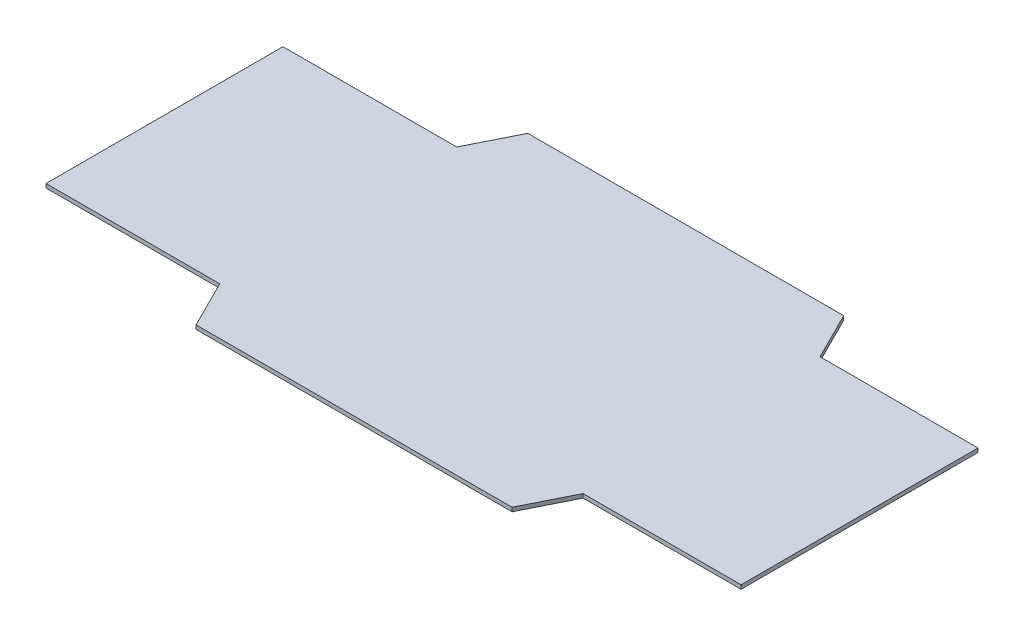
SolidWorks part; units mm, degrees
ref_plane "Front Plane" through (0, 0, 0) normal (0, 0, 1) x (1, 0, 0)
ref_plane "Top Plane" through (0, 0, 0) normal (0, 1, 0) x (1, 0, 0)
ref_plane "Right Plane" through (0, 0, 0) normal (1, 0, 0) x (0, 0, -1)
sketch "Sketch3" plane through (0, 0, 0) normal (0, 1, 0) x (1, 0, 0)
  line L0 (-279.4, 95.25) -> (-139.7, 95.25)
  line L1 (-279.4, -133.35) -> (279.4, -133.35) construction
  line L2 (-279.4, -133.35) -> (-279.4, 133.35) construction
  line L3 (-279.4, 133.35) -> (279.4, 133.35) construction
  line L4 (279.4, -133.35) -> (279.4, 133.35) construction
  line L5 (-279.4, -133.35) -> (279.4, 133.35) construction
  line L6 (-279.4, 133.35) -> (279.4, -133.35) construction
  line L7 (-279.4, -95.25) -> (279.4, -95.25) construction
  line L8 (-279.4, -95.25) -> (-279.4, 95.25) construction
  line L9 (-279.4, 95.25) -> (279.4, 95.25) construction
  line L10 (279.4, -95.25) -> (279.4, 95.25) construction
  line L13 (-139.7, 95.25) -> (-120.65, 133.35)
  line L14 (-120.65, 133.35) -> (133.35, 133.35)
  line L15 (133.35, 133.35) -> (152.4, 95.25)
  line L16 (152.4, 95.25) -> (279.4, 95.25)
  line L17 (-279.4, 95.25) -> (-279.4, -95.25)
  line L18 (279.4, 95.25) -> (279.4, -95.25)
  line L19 (-279.4, 0) -> (279.4, 0) construction
  line L20 (152.4, -95.25) -> (279.4, -95.25)
  line L21 (133.35, -133.35) -> (152.4, -95.25)
  line L22 (-120.65, -133.35) -> (133.35, -133.35)
  line L23 (-139.7, -95.25) -> (-120.65, -133.35)
  line L24 (-279.4, -95.25) -> (-139.7, -95.25)
  point P0 (0, 0)
  point P6 (0, 0)
  dimension "D1" = 266.7
  dimension "D2" = 558.8
  dimension "D3" = 190.5
  dimension "D4" = 127
  dimension "D5" = 139.7
  dimension "D6" = 254
extrude "Boss-Extrude1" add sketch "Sketch3" along normal mid plane 3.175
sketch "Sketch5" plane through (0, -1.5875, 0) normal (0, -1, 0) x (1, 0, 0)
  line L0 (-202.3532, 0) -> (279.4, 0) construction
  line L1 (-63.5, 25.4) -> (76.2, 25.4)
  line L2 (-63.5, 25.4) -> (-63.5, 88.9)
  line L3 (-63.5, 88.9) -> (76.2, 88.9)
  line L4 (76.2, 25.4) -> (76.2, 88.9)
  line L5 (-63.5, 25.4) -> (76.2, 88.9) construction
  line L6 (-63.5, 88.9) -> (76.2, 25.4) construction
  line L7 (279.4, 95.25) -> (279.4, -95.25) construction
  line L8 (-120.65, 133.35) -> (133.35, 133.35) construction
  line L9 (-120.65, 133.35) -> (133.35, 133.35) construction
  line L10 (6.35, 133.35) -> (6.35, 88.9) construction
  line L11 (-63.5, -88.9) -> (76.2, -88.9)
  line L12 (76.2, -25.4) -> (76.2, -88.9)
  line L13 (-63.5, -25.4) -> (76.2, -25.4)
  line L14 (-63.5, -25.4) -> (-63.5, -88.9)
  point P4 (6.35, 57.15)
  dimension "D1" = 63.5
  dimension "D2" = 139.7
  dimension "D3" = 44.45
sketch "Sketch6" plane through (0, 1.5875, 0) normal (0, 1, 0) x (1, 0, 0)
  line L0 (-279.4, 95.25) -> (-139.7, 95.25) construction
  line L1 (-120.65, 133.35) -> (-139.7, 95.25) construction
  line L2 (-139.7, 95.25) -> (-279.4, 95.25) construction
  line L3 (-139.7, 95.25) -> (-120.65, 133.35) construction
  line L4 (-120.65, 133.35) -> (133.35, 133.35) construction
  line L5 (133.35, 133.35) -> (152.4, 95.25) construction
  line L6 (152.4, 95.25) -> (279.4, 95.25) construction
  line L7 (279.4, 95.25) -> (279.4, -95.25) construction
  line L8 (279.4, -95.25) -> (152.4, -95.25) construction
  line L9 (133.35, -133.35) -> (152.4, -95.25) construction
  line L10 (152.4, -95.25) -> (279.4, -95.25) construction
  line L11 (152.4, -95.25) -> (133.35, -133.35) construction
  line L12 (133.35, -133.35) -> (-120.65, -133.35) construction
  line L13 (-120.65, -133.35) -> (-139.7, -95.25) construction
  line L14 (-139.7, -95.25) -> (-279.4, -95.25) construction
  line L15 (-279.4, -95.25) -> (-279.4, 95.25) construction
  line L16 (-276.225, 92.075) -> (-137.7377, 92.075)
  line L17 (-137.7377, 92.075) -> (-118.6877, 130.175)
  line L18 (-118.6877, 130.175) -> (131.3877, 130.175)
  line L19 (131.3877, 130.175) -> (150.4377, 92.075)
  line L20 (150.4377, 92.075) -> (276.225, 92.075)
  line L21 (276.225, 92.075) -> (276.225, -92.075)
  line L22 (276.225, -92.075) -> (150.4377, -92.075)
  line L23 (150.4377, -92.075) -> (131.3877, -130.175)
  line L24 (131.3877, -130.175) -> (-118.6877, -130.175)
  line L25 (-118.6877, -130.175) -> (-137.7377, -92.075)
  line L26 (-137.7377, -92.075) -> (-276.225, -92.075)
  line L27 (-276.225, -92.075) -> (-276.225, 92.075)
  dimension "D1" = 3.175
sketch "Sketch7" plane through (0, 1.5875, 0) normal (0, 1, 0) x (1, 0, 0)
  line L0 (279.4, 95.25) -> (279.4, -95.25) construction
  circle A0 centre (203.2, 0) radius 44.45
  dimension "D1" = 88.9
  dimension "D2" = 76.2
